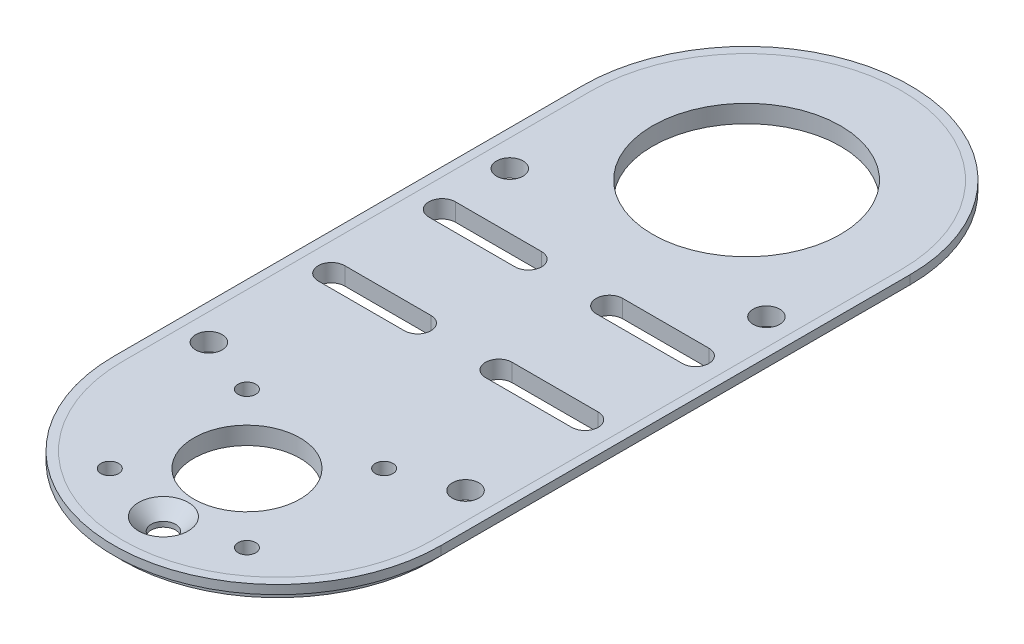
SolidWorks part; units mm, degrees
ref_plane "Alzado" through (0, 0, 0) normal (0, 0, 1) x (1, 0, 0)
ref_plane "Planta" through (0, 0, 0) normal (0, 1, 0) x (1, 0, 0)
ref_plane "Vista lateral" through (0, 0, 0) normal (1, 0, 0) x (0, 0, -1)
sketch "Croquis1" plane through (0, 0, 0) normal (0, 1, 0) x (1, 0, 0)
  line L0 (0, 88.0043) -> (0, -17.9957)
  line L2 (-35, 88.0043) -> (-35, -17.9957)
  line L4 (35, 88.0043) -> (35, -17.9957)
  arc A0 (-35, 88.0043) -> (35, 88.0043) centre (0, 88.0043) cw
  arc A1 (-35, -17.9957) -> (35, -17.9957) centre (0, -17.9957) ccw
  point P0 (0, 0)
  dimension "D2" = 35
  dimension "D3" = 106
extrude "Saliente-Extruir1" add sketch "Croquis1" along normal blind 4
sketch "Croquis3" plane through (0, 4, 0) normal (0, 1, 0) x (1, 0, 0)
  line L0 (-37, 88.0043) -> (-37, -17.9957)
  line L1 (37, -17.9957) -> (37, 88.0043)
  line L2 (-35, 88.0043) -> (-35, -17.9957)
  line L3 (35, -17.9957) -> (35, 88.0043)
  line L4 (-35, 88.0043) -> (-35, -17.9957)
  line L5 (35, -17.9957) -> (35, 88.0043)
  arc A0 (-37, -17.9957) -> (37, -17.9957) centre (0, -17.9957) ccw
  arc A1 (37, 88.0043) -> (-37, 88.0043) centre (0, 88.0043) ccw
  arc A2 (-35, -17.9957) -> (35, -17.9957) centre (0, -17.9957) ccw
  arc A3 (35, 88.0043) -> (-35, 88.0043) centre (0, 88.0043) ccw
  arc A4 (-35, -17.9957) -> (35, -17.9957) centre (0, -17.9957) ccw
  arc A5 (35, 88.0043) -> (-35, 88.0043) centre (0, 88.0043) ccw
  dimension "D1" = 0
  dimension "D2" = 2
extrude "Saliente-Extruir2" add sketch "Croquis3" against normal blind 2 separate body
sketch "Croquis4" plane through (0, 4, 0) normal (0, 1, 0) x (1, 0, 0)
  line L0 (0, -54.9957) -> (0, 125.0043) construction
  line L1 (37, 35.0043) -> (-37, 35.0043) construction
  line L2 (37, -17.9957) -> (37, 88.0043) construction
  line L3 (-37, 88.0043) -> (-37, -17.9957) construction
  line L4 (-29, 35.0043) -> (-29, 63.5043) construction
  line L5 (-29, 35.0043) -> (-29, -4.4957) construction
  line L7 (-15.5, -9.3963) -> (15.5, -9.3963)
  line L8 (-15.5, -9.3963) -> (-15.5, -40.3963)
  line L9 (-15.5, -40.3963) -> (15.5, -40.3963)
  line L10 (15.5, -9.3963) -> (15.5, -40.3963)
  line L11 (-15.5, -9.3963) -> (15.5, -40.3963) construction
  line L12 (-15.5, -40.3963) -> (15.5, -9.3963) construction
  arc A0 (-37, -17.9957) -> (37, -17.9957) centre (0, -17.9957) ccw construction
  arc A1 (37, 88.0043) -> (-37, 88.0043) centre (0, 88.0043) ccw construction
  circle A2 centre (-29, 63.5043) radius 3
  circle A3 centre (-29, -4.4957) radius 3
  circle A4 centre (29, -4.4957) radius 3
  circle A5 centre (29, 63.5043) radius 3
  circle A6 centre (0, -43.7757) radius 3
  circle A7 centre (0, 88.0043) radius 21.25
  circle A8 centre (0, -24.8963) radius 12
  circle A9 centre (-15.5, -9.3963) radius 2
  circle A10 centre (-15.5, -40.3963) radius 2
  circle A11 centre (15.5, -9.3963) radius 2
  circle A12 centre (15.5, -40.3963) radius 2
  dimension "D4" = 6
  dimension "D5" = 6
  dimension "D6" = 6
  dimension "D9" = 42.5
  dimension "D10" = 24
  dimension "D13" = 4
  dimension "D1" = 28.5
  dimension "D2" = 8
  dimension "D3" = 39.5
  dimension "D7" = 11.22
  dimension "D8" = 37
  dimension "D11" = 31
  dimension "D12" = 31
extrude "Cortar-Extruir1" cut sketch "Croquis4" against normal blind 10 contours A7 | A2 | A5 | A4 | A3 | A9 | A10 | A12 | A8 | A11
sketch "Croquis9" plane through (0, 4, 0) normal (0, 1, 0) x (1, 0, 0)
  line L0 (0, -54.9957) -> (0, -43.7757) construction
  arc A0 (-37, -17.9957) -> (37, -17.9957) centre (0, -17.9957) ccw construction
  dimension "D1" = 11.22
hole_wizard "Refrentado para tornillo tapón con cabeza plana de clavija de M51" positions "Croquis11" profile "Croquis10" countersink size "M5" standard "Ansi Metric" end condition through all
sketch "Croquis11" plane through (0, 4, 0) normal (0, 1, 0) x (1, 0, 0)
  point P0 (0, -43.7757)
sketch "Croquis10" plane through (0, 4, 43.7757) normal (1, 0, 0) x (0, 0, 1)
  line L0 (0, 0) -> (0, 4)
  line L1 (0, 4) -> (2.75, 4)
  line L2 (2.75, 4) -> (2.75, 2.85)
  line L3 (2.75, 2.85) -> (5.6, 0)
  line L5 (5.6, 0) -> (0, 0)
  line L6 (-2.75, 2.85) -> (-5.6, 0) construction
  line L11 (0, -6.35) -> (0, 107.95) construction
  dimension "Diámetro de taladro hasta el siguiente" = 5.5
  dimension "Profundidad de taladro hasta el siguiente" = 4
  dimension "Diámetro de avellanado cercano" = 11.2
  dimension "Ángulo de avellanado cercano" = 90
sketch "Croquis12" plane through (0, 4, 0) normal (0, 1, 0) x (1, 0, 0)
  line L0 (0, -54.9957) -> (0, 125.0043) construction
  line L1 (-37, 35.0043) -> (37, 35.0043) construction
  line L2 (-37, 88.0043) -> (-37, -17.9957) construction
  line L3 (37, -17.9957) -> (37, 88.0043) construction
  line L4 (-37, 23.0043) -> (-31.64, 23.0043) construction
  line L5 (0, -54.9957) -> (-71.4487, -54.9957) construction
  line L6 (-28.6439, 22.8518) -> (-9.1639, 22.8518) construction
  line L7 (-28.6439, 25.8518) -> (-9.1639, 25.8518)
  line L8 (-28.6439, 19.8518) -> (-9.1639, 19.8518)
  line L9 (-18.9039, 22.8518) -> (-18.9039, 35.3518) construction
  line L10 (-18.9039, 35.3518) -> (-9.1639, 35.3518) construction
  line L11 (-28.6439, 47.8518) -> (-9.1639, 47.8518) construction
  line L12 (-28.6439, 44.8518) -> (-9.1639, 44.8518)
  line L13 (-28.6439, 50.8518) -> (-9.1639, 50.8518)
  line L14 (28.6439, 22.8518) -> (9.1639, 22.8518) construction
  line L15 (28.6439, 25.8518) -> (9.1639, 25.8518)
  line L16 (28.6439, 19.8518) -> (9.1639, 19.8518)
  line L17 (28.6439, 47.8518) -> (9.1639, 47.8518) construction
  line L18 (28.6439, 44.8518) -> (9.1639, 44.8518)
  line L19 (28.6439, 50.8518) -> (9.1639, 50.8518)
  arc A0 (-37, -17.9957) -> (37, -17.9957) centre (0, -17.9957) ccw construction
  arc A1 (37, 88.0043) -> (-37, 88.0043) centre (0, 88.0043) ccw construction
  arc A2 (-28.6439, 25.8518) -> (-28.6439, 19.8518) centre (-28.6439, 22.8518) ccw
  arc A3 (-9.1639, 19.8518) -> (-9.1639, 25.8518) centre (-9.1639, 22.8518) ccw
  arc A4 (-28.6439, 44.8518) -> (-28.6439, 50.8518) centre (-28.6439, 47.8518) cw
  arc A5 (-9.1639, 50.8518) -> (-9.1639, 44.8518) centre (-9.1639, 47.8518) cw
  arc A6 (28.6439, 25.8518) -> (28.6439, 19.8518) centre (28.6439, 22.8518) cw
  arc A7 (9.1639, 19.8518) -> (9.1639, 25.8518) centre (9.1639, 22.8518) cw
  arc A8 (28.6439, 44.8518) -> (28.6439, 50.8518) centre (28.6439, 47.8518) ccw
  arc A9 (9.1639, 50.8518) -> (9.1639, 44.8518) centre (9.1639, 47.8518) ccw
  point P19 (-18.9039, 22.8518)
  point P29 (-18.9039, 47.8518)
  point P36 (18.9039, 22.8518)
  point P43 (18.9039, 47.8518)
  dimension "D3" = 3
  dimension "D1" = 5.36
  dimension "D2" = 78
  dimension "D4" = 19.48
  dimension "D5" = 12.5
extrude "Cortar-Extruir2" cut sketch "Croquis12" against normal blind 10
